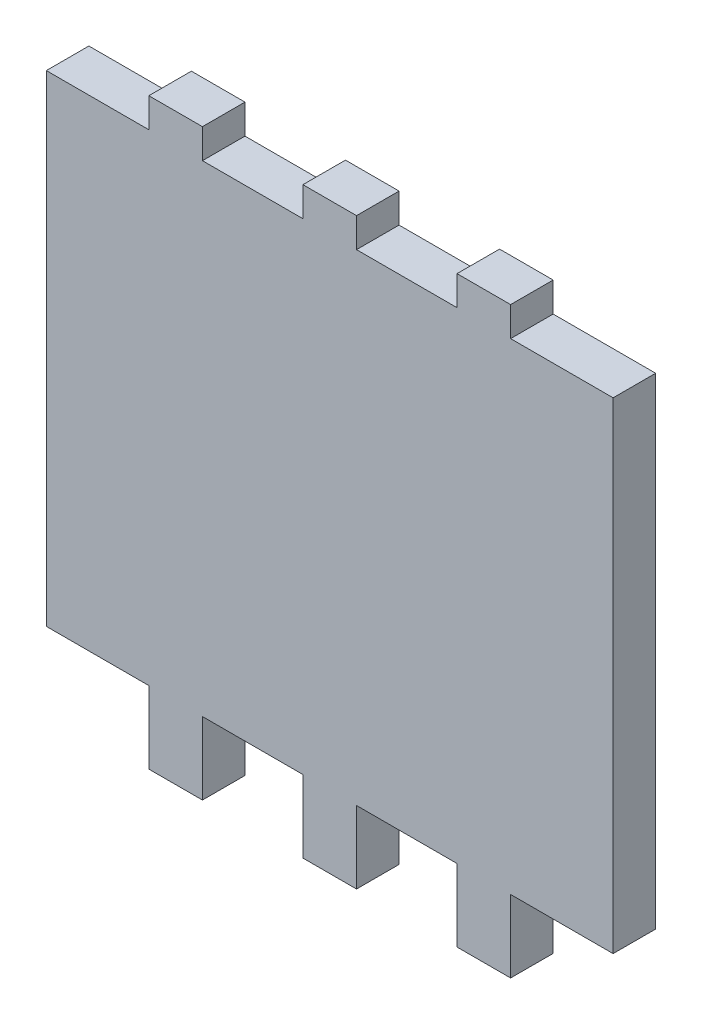
SolidWorks part; units mm, degrees
ref_plane "Front Plane" through (0, 0, 0) normal (0, 0, 1) x (1, 0, 0)
ref_plane "Top Plane" through (0, 0, 0) normal (0, 1, 0) x (1, 0, 0)
ref_plane "Right Plane" through (0, 0, 0) normal (1, 0, 0) x (0, 0, -1)
sketch "Sketch1" plane through (0, 0, 0) normal (0, 0, 1) x (1, 0, 0)
  line L0 (-21.15, 21.7625) -> (21.15, 21.7625) construction
  line L1 (-21.15, 43.525) -> (21.15, 43.525)
  line L2 (-21.15, 43.525) -> (-21.15, 0)
  line L3 (-21.15, 0) -> (21.15, 0)
  line L4 (21.15, 43.525) -> (21.15, 0)
  line L5 (-13.5, 43.525) -> (-9.5, 43.525)
  line L6 (-13.5, 43.525) -> (-13.5, 41.325)
  line L8 (-9.5, 43.525) -> (-9.5, 41.325)
  line L9 (-2, 43.525) -> (2, 43.525)
  line L10 (-2, 43.525) -> (-2, 41.325)
  line L11 (-2, 41.325) -> (2, 41.325)
  line L12 (2, 43.525) -> (2, 41.325)
  line L13 (9.5, 43.525) -> (13.5, 43.525)
  line L14 (9.5, 43.525) -> (9.5, 41.325)
  line L15 (9.5, 41.325) -> (13.5, 41.325)
  line L16 (13.5, 43.525) -> (13.5, 41.325)
  line L17 (13.5, 0) -> (13.5, 2.2)
  line L18 (9.5, 2.2) -> (13.5, 2.2)
  line L19 (9.5, 0) -> (9.5, 2.2)
  line L20 (2, 0) -> (2, 2.2)
  line L21 (-2, 2.2) -> (2, 2.2)
  line L22 (-2, 0) -> (-2, 2.2)
  line L23 (-13.5, 2.2) -> (-9.5, 2.2)
  line L24 (-9.5, 0) -> (-9.5, 2.2)
  line L25 (-13.5, 0) -> (-13.5, 2.2)
  line L26 (-13.5, 3.2) -> (-13.5, 5.4)
  line L27 (-9.5, 3.2) -> (-9.5, 5.4)
  line L28 (-13.5, 5.4) -> (-9.5, 5.4)
  line L29 (-2, 3.2) -> (-2, 5.4)
  line L30 (-2, 5.4) -> (2, 5.4)
  line L31 (2, 3.2) -> (2, 5.4)
  line L32 (9.5, 3.2) -> (9.5, 5.4)
  line L33 (9.5, 5.4) -> (13.5, 5.4)
  line L34 (13.5, 3.2) -> (13.5, 5.4)
  line L35 (-21.15, 5.4) -> (21.15, 5.4)
  line L36 (21.15, 41.325) -> (-9.5, 41.325)
  line L37 (-13.5, 41.325) -> (-21.15, 41.325)
  line L38 (-13.5, 5.4) -> (-13.5, 0)
  line L39 (-9.5, 5.4) -> (-9.5, 0)
  line L40 (-2, 0) -> (-2, 5.4)
  line L41 (2, 5.4) -> (2, 0)
  line L42 (9.5, 0) -> (9.5, 5.4)
  line L43 (13.5, 5.4) -> (13.5, 0)
  point P4 (0, 0)
  point P10 (-9.5, 42.425)
  point P20 (2, 42.425)
  point P21 (13.5, 42.425)
  dimension "D1" = 42.3
  dimension "D2" = 43.525
  dimension "D3" = 4
  dimension "D5" = 4
  dimension "D6" = 4
  dimension "D7" = 7.5
  dimension "D8" = 7.5
  dimension "D9" = 7.65
  dimension "D4" = 5.4
  dimension "D10" = 2
extrude "Boss-Extrude1" add sketch "Sketch1" along normal blind 3.175 contours L25 L3 L24 L23 | L39 L27 L28 L26 L38 L23 | L41 L31 L30 L29 L40 L21 | L22 L3 L20 L21 | L19 L3 L17 L18 | L43 L34 L33 L32 L42 L18 | L0 L2 L35 L28 L30 L33 L4 | L2 L0 L4 L36 L15 L11 L8 L1 L6 L37 | L12 L1 L10 L11 | L16 L1 L14 L15
equation "\"motor width\"=4.23"
equation "\"D1@Sketch1\"=\"motor width\""
equation "\"motor height\"=4.3525"
equation "\"D2@Sketch1\"=\"motor height\""
equation "\"tooth width\"=0.4"
equation "\"D3@Sketch1\"=\"tooth width\""
equation "\"width\"=0.3175"
equation "\"D5@Sketch1\"=\"tooth width\""
equation "\"D6@Sketch1\"=\"tooth width\""
equation "\"teeth distance\"=0.75"
equation "\"D7@Sketch1\"=\"teeth distance\""
equation "\"D8@Sketch1\"=\"teeth distance\""
